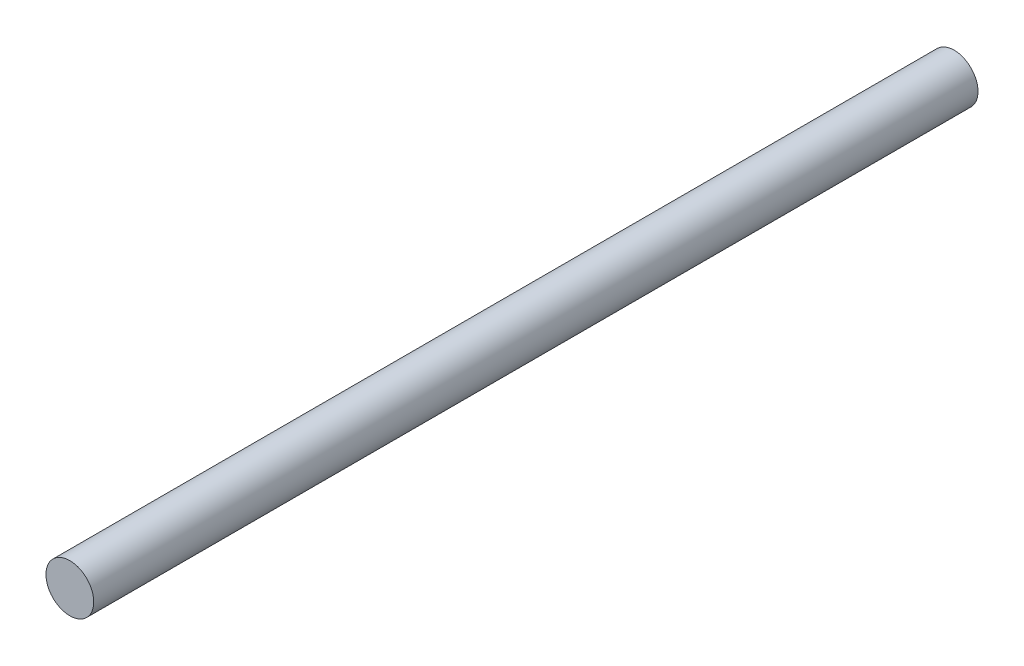
SolidWorks part; units mm, degrees
material "1060 Alloy"
ref_plane "Front Plane" through (0, 0, 0) normal (0, 0, 1) x (1, 0, 0)
ref_plane "Top Plane" through (0, 0, 0) normal (0, 1, 0) x (1, 0, 0)
ref_plane "Right Plane" through (0, 0, 0) normal (1, 0, 0) x (0, 0, -1)
sketch "Sketch1" plane through (0, 0, 0) normal (0, 0, 1) x (1, 0, 0)
  circle A0 centre (0, 0) radius 2
  dimension "D1" = 4
extrude "Boss-Extrude1" add sketch "Sketch1" along normal blind 74
sketch "Sketch2" plane through (0, 0, 0) normal (0, 0, -1) x (-1, 0, 0)
  point P0 (0, 0)
